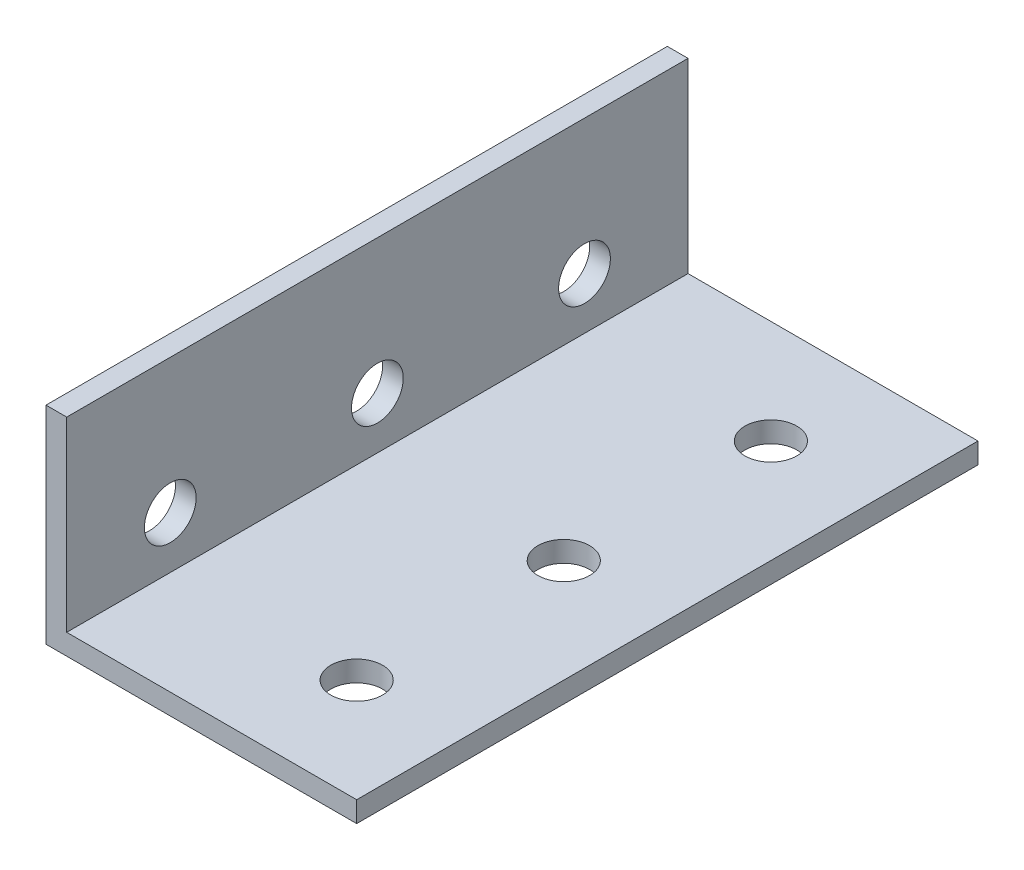
SolidWorks part; units mm, degrees
ref_plane "Front Plane" through (0, 0, 0) normal (0, 0, 1) x (1, 0, 0)
ref_plane "Top Plane" through (0, 0, 0) normal (0, 1, 0) x (1, 0, 0)
ref_plane "Right Plane" through (0, 0, 0) normal (1, 0, 0) x (0, 0, -1)
sketch "Sketch1" plane through (0, 0, 0) normal (0, 0, 1) x (1, 0, 0)
  line L0 (0, 0) -> (0, 20)
  line L1 (0, 20) -> (2, 20)
  line L2 (2, 20) -> (2, 2)
  line L3 (2, 2) -> (30, 2)
  line L4 (30, 2) -> (30, 0)
  line L5 (30, 0) -> (0, 0)
  dimension "D1" = 20
  dimension "D2" = 30
  dimension "D3" = 2
  dimension "D4" = 2
extrude "Boss-Extrude1" add sketch "Sketch1" along normal blind 60
sketch "Sketch2" plane through (0, 2, 0) normal (0, 1, 0) x (1, 0, 0)
  line L0 (2, -60) -> (2, 0) construction
  circle A0 centre (20, -30) radius 2.5
  circle A1 centre (20, -10) radius 2.5
  circle A2 centre (20, -50) radius 2.5
  dimension "D1" = 20
  dimension "D2" = 20
  dimension "D3" = 18
  dimension "D4" = 18
  dimension "D5" = 18
extrude "Cut-Extrude1" cut sketch "Sketch2" against normal blind 10
sketch "Sketch3" plane through (2, 0, 0) normal (1, 0, 0) x (0, 0, -1)
  line L3 (-30, 20) -> (-30, 2) construction
  line L4 (-60, 20) -> (0, 20) construction
  line L5 (-60, 2) -> (0, 2) construction
  circle A0 centre (-30, 7) radius 2.5
  circle A1 centre (-10, 7) radius 2.5
  circle A2 centre (-50, 7) radius 2.5
  dimension "D1" = 20
  dimension "D2" = 20
  dimension "D3" = 5
  dimension "D4" = 5
  dimension "D5" = 5
extrude "Cut-Extrude2" cut sketch "Sketch3" against normal blind 10
